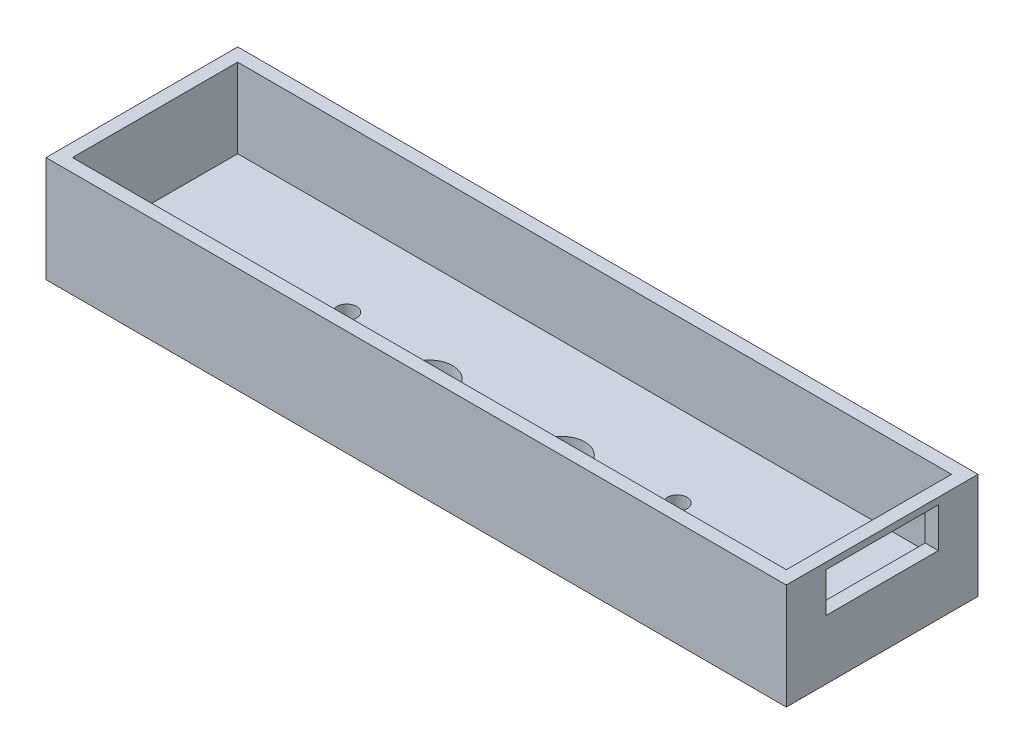
SolidWorks part; units mm, degrees
ref_plane "Front Plane" through (0, 0, 0) normal (0, 0, 1) x (1, 0, 0)
ref_plane "Top Plane" through (0, 0, 0) normal (0, 1, 0) x (1, 0, 0)
ref_plane "Right Plane" through (0, 0, 0) normal (1, 0, 0) x (0, 0, -1)
sketch "Sketch1" plane through (0, 0, 0) normal (0, 1, 0) x (1, 0, 0)
  line L1 (-42.4555, 18.7875) -> (65.5445, 18.7875)
  line L2 (-42.4555, 18.7875) -> (-42.4555, -6.2125)
  line L3 (-42.4555, -6.2125) -> (65.5445, -6.2125)
  line L4 (65.5445, 18.7875) -> (65.5445, -6.2125)
  dimension "D1" = 108
  dimension "D2" = 25
extrude "Boss-Extrude1" add sketch "Sketch1" along normal blind 4
sketch "Sketch2" plane through (0, 4, 0) normal (0, 1, 0) x (1, 0, 0)
  line L0 (-42.4555, 18.7875) -> (-42.4555, -6.2125) construction
  line L1 (65.5445, 18.7875) -> (-42.4555, 18.7875) construction
  circle A0 centre (-13.4555, 6.2875) radius 1.5
  circle A1 centre (36.5445, 6.2875) radius 1.5
  dimension "D1" = 3
  dimension "D2" = 3
  dimension "D3" = 50
  dimension "D4" = 29
  dimension "D5" = 12.5
  dimension "D6" = 12.5
extrude "Cut-Extrude1" cut sketch "Sketch2" against normal up to next
sketch "Sketch3" plane through (0, 0, 0) normal (0, -1, 0) x (-1, 0, 0)
  circle A0 centre (-36.5445, 6.2875) radius 3.5
  circle A1 centre (13.4555, 6.2875) radius 3.5
  circle A2 centre (-36.5445, 6.2875) radius 1.5 construction
  circle A3 centre (13.4555, 6.2875) radius 1.5 construction
  circle M3 centre (13.4555, 6.2875) radius 1.5
  dimension "D1" = 7
  dimension "D2" = 7
extrude "Cut-Extrude3" cut sketch "Sketch3" against normal blind 2 contours A1 M3 | A0
sketch "Sketch4" plane through (0, 4, 0) normal (0, 1, 0) x (1, 0, 0)
  line L0 (65.5445, -6.2125) -> (65.5445, 18.7875) construction
  line L1 (-42.4555, -6.2125) -> (65.5445, -6.2125) construction
  circle A0 centre (21.5445, 3.7875) radius 1.25
  circle A1 centre (1.5445, 3.7875) radius 1.25
  dimension "D1" = 2.5
  dimension "D2" = 2.5
  dimension "D3" = 20
  dimension "D4" = 44
  dimension "D5" = 10
  dimension "D6" = 10
extrude "Cut-Extrude4" cut sketch "Sketch4" against normal up to next
sketch "Sketch5" plane through (0, 4, 0) normal (0, 1, 0) x (1, 0, 0)
  circle A0 centre (21.5445, 3.7875) radius 3.5
  circle A1 centre (1.5445, 3.7875) radius 3.5
  circle A2 centre (21.5445, 3.7875) radius 1.25 construction
  circle A3 centre (1.5445, 3.7875) radius 1.25 construction
  dimension "D1" = 7
  dimension "D2" = 7
extrude "Cut-Extrude5" cut sketch "Sketch5" against normal blind 1.7
sketch "Sketch6" plane through (0, 4, 0) normal (0, 1, 0) x (1, 0, 0)
  line L0 (-42.4555, -6.2125) -> (65.5445, -6.2125) construction
  line L1 (67.5445, 18.7875) -> (65.5445, 18.7875)
  line L2 (67.5445, 18.7875) -> (67.5445, -6.2125)
  line L3 (67.5445, -6.2125) -> (65.5445, -6.2125)
  line L4 (65.5445, 18.7875) -> (65.5445, -6.2125)
  line L5 (67.5445, -6.2125) -> (-44.4555, -6.2125)
  line L6 (67.5445, -6.2125) -> (67.5445, -8.2125)
  line L7 (67.5445, -8.2125) -> (-44.4555, -8.2125)
  line L8 (-44.4555, -6.2125) -> (-44.4555, -8.2125)
  line L9 (-44.4555, -6.2125) -> (-42.4555, -6.2125)
  line L10 (-44.4555, -6.2125) -> (-44.4555, 18.7875)
  line L11 (-44.4555, 18.7875) -> (-42.4555, 18.7875)
  line L12 (-42.4555, -6.2125) -> (-42.4555, 18.7875)
  line L13 (67.5445, 20.7875) -> (-44.4555, 20.7875)
  line L14 (67.5445, 20.7875) -> (67.5445, 18.7875)
  line L15 (67.5445, 18.7875) -> (-44.4555, 18.7875)
  line L16 (-44.4555, 20.7875) -> (-44.4555, 18.7875)
  line L17 (65.5445, -6.2125) -> (65.5445, 18.7875) construction
  line L18 (65.5445, 18.7875) -> (-42.4555, 18.7875) construction
  line L19 (-42.4555, 18.7875) -> (-42.4555, -6.2125) construction
  line M20 (-42.4555, 18.7875) -> (-42.4555, -6.2125)
  line M21 (-42.4555, -6.2125) -> (65.5445, -6.2125)
  line M23 (65.5445, 18.7875) -> (-42.4555, 18.7875)
  dimension "D1" = 2
  dimension "D2" = 2
  dimension "D3" = 2
  dimension "D4" = 2
  dimension "D5" = 2
  dimension "D6" = 0
  dimension "D7" = 0
  dimension "D8" = 0
  dimension "D9" = 0
  dimension "D10" = 2
  dimension "D11" = 0
  dimension "D12" = 0
  dimension "D13" = 2
  dimension "D14" = 0
  dimension "D15" = 2
  dimension "D16" = 0
extrude "Boss-Extrude2" add sketch "Sketch6" along normal blind 12 and the other way blind 4 contours L13 L16 L11 L1 L14 M23 | L5 L8 L7 L6 L3 M21 | L11 L10 L5 M20
sketch "Sketch10" plane through (67.5445, 0, 0) normal (1, 0, 0) x (0, 0, -1)
  line L0 (-2.2125, 9) -> (14.7875, 9)
  line L5 (-2.2125, 9) -> (-2.2125, 15)
  line L6 (-2.2125, 15) -> (14.7875, 15)
  line L7 (14.7875, 9) -> (14.7875, 15)
  line L8 (20.7875, 16) -> (-8.2125, 16) construction
  line L9 (20.7875, 0) -> (20.7875, 16) construction
  point P8 (0, 0)
  point P9 (0, 0)
  point P10 (0, 0)
  dimension "D1" = 6
  dimension "D2" = 17
  dimension "D3" = 1
  dimension "D4" = 6
extrude "Cut-Extrude8" cut sketch "Sketch10" against normal up to next
